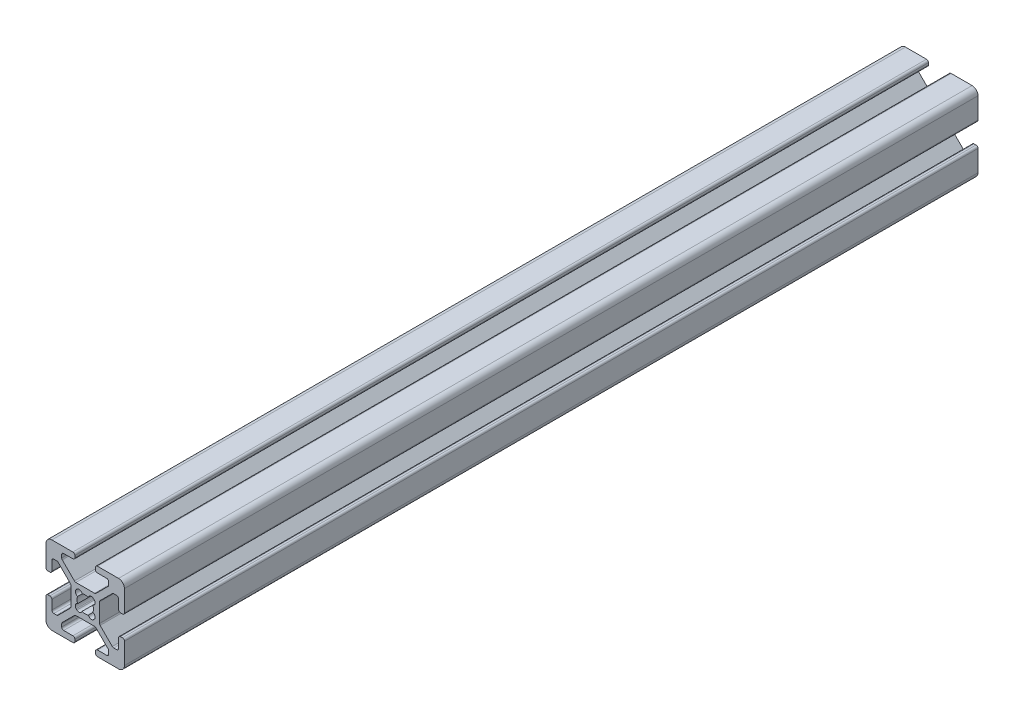
SolidWorks part; units mm, degrees
ref_plane "Front Plane" through (0, 0, 0) normal (0, 0, 1) x (1, 0, 0)
ref_plane "Top Plane" through (0, 0, 0) normal (0, 1, 0) x (1, 0, 0)
ref_plane "Right Plane" through (0, 0, 0) normal (1, 0, 0) x (0, 0, -1)
ref_plane "Plane1" through (0, 0, -4000) normal (0, 0, -1) x (-1, 0, 0)
sketch "Sketch1" plane through (0, 0, -4000) normal (0, 0, -1) x (-1, 0, 0)
  line L0 (2.3045, -2.1245) -> (2.1245, -2.3045)
  line L1 (-2.1245, -2.3045) -> (-2.3045, -2.1245)
  line L2 (-2.3045, 2.1245) -> (-2.1245, 2.3045)
  line L3 (2.1245, 2.3045) -> (2.3045, 2.1245)
  line L4 (10, -8.5) -> (10, -3.138)
  line L5 (9.492, -2.63) -> (9.008, -2.63)
  line L6 (8.5, -3.138) -> (8.5, -5.487)
  line L7 (7.992, -5.995) -> (7.2659, -5.995)
  line L8 (6.9067, -5.8462) -> (3.8038, -2.7433)
  line L9 (3.655, -2.3841) -> (3.655, 2.3838)
  line L10 (3.8038, 2.743) -> (6.907, 5.8462)
  line L11 (7.2662, 5.995) -> (7.992, 5.995)
  line L12 (8.5, 5.487) -> (8.5, 3.138)
  line L13 (9.008, 2.63) -> (9.492, 2.63)
  line L14 (10, 3.138) -> (10, 8.5)
  line L15 (8.5, 10) -> (3.138, 10)
  line L16 (2.63, 9.492) -> (2.63, 9.008)
  line L17 (3.138, 8.5) -> (5.487, 8.5)
  line L18 (5.995, 7.992) -> (5.995, 7.2659)
  line L19 (5.8462, 6.9067) -> (2.7433, 3.8038)
  line L20 (2.3841, 3.655) -> (-2.3838, 3.655)
  line L21 (-2.743, 3.8038) -> (-5.8462, 6.907)
  line L22 (-5.995, 7.2662) -> (-5.995, 7.992)
  line L23 (-5.487, 8.5) -> (-3.138, 8.5)
  line L24 (-2.63, 9.008) -> (-2.63, 9.492)
  line L25 (-3.138, 10) -> (-8.5, 10)
  line L26 (-10, 8.5) -> (-10, 3.138)
  line L27 (-9.492, 2.63) -> (-9.008, 2.63)
  line L28 (-8.5, 3.138) -> (-8.5, 5.487)
  line L29 (-7.992, 5.995) -> (-7.2659, 5.995)
  line L30 (-6.9067, 5.8462) -> (-3.8038, 2.7433)
  line L31 (-3.655, 2.3841) -> (-3.655, -2.3838)
  line L32 (-3.8038, -2.743) -> (-6.907, -5.8462)
  line L33 (-7.2662, -5.995) -> (-7.992, -5.995)
  line L34 (-8.5, -5.487) -> (-8.5, -3.138)
  line L35 (-9.008, -2.63) -> (-9.492, -2.63)
  line L36 (-10, -3.138) -> (-10, -8.5)
  line L37 (-8.5, -10) -> (-3.138, -10)
  line L38 (-2.63, -9.492) -> (-2.63, -9.008)
  line L39 (-3.138, -8.5) -> (-5.487, -8.5)
  line L40 (-5.995, -7.992) -> (-5.995, -7.2659)
  line L41 (-5.8462, -6.9067) -> (-2.7433, -3.8038)
  line L42 (-2.3841, -3.655) -> (2.3838, -3.655)
  line L43 (2.743, -3.8038) -> (5.8462, -6.907)
  line L44 (5.995, -7.2662) -> (5.995, -7.992)
  line L45 (5.487, -8.5) -> (3.138, -8.5)
  line L46 (2.63, -9.008) -> (2.63, -9.492)
  line L47 (3.138, -10) -> (8.5, -10)
  arc A0 (1.9358, 0.8037) -> (1.9358, -0.8037) centre (0, 0) cw
  arc A1 (1.9358, -0.8037) -> (2.3045, -2.1245) centre (1.748, -1.568) cw
  arc A2 (2.1245, -2.3045) -> (0.8037, -1.9358) centre (1.568, -1.748) cw
  arc A3 (0.8037, -1.9358) -> (-0.8037, -1.9358) centre (0, 0) cw
  arc A4 (-0.8037, -1.9358) -> (-2.1245, -2.3045) centre (-1.568, -1.748) cw
  arc A5 (-2.3045, -2.1245) -> (-1.9358, -0.8037) centre (-1.748, -1.568) cw
  arc A6 (-1.9358, -0.8037) -> (-1.9358, 0.8037) centre (0, 0) cw
  arc A7 (-1.9358, 0.8037) -> (-2.3045, 2.1245) centre (-1.748, 1.568) cw
  arc A8 (-2.1245, 2.3045) -> (-0.8037, 1.9358) centre (-1.568, 1.748) cw
  arc A9 (-0.8037, 1.9358) -> (0.8037, 1.9358) centre (0, 0) cw
  arc A10 (0.8037, 1.9358) -> (2.1245, 2.3045) centre (1.568, 1.748) cw
  arc A11 (2.3045, 2.1245) -> (1.9358, 0.8037) centre (1.748, 1.568) cw
  arc A12 (10, -3.138) -> (9.492, -2.63) centre (9.492, -3.138) ccw
  arc A13 (9.008, -2.63) -> (8.5, -3.138) centre (9.008, -3.138) ccw
  arc A14 (8.5, -5.487) -> (7.992, -5.995) centre (7.992, -5.487) cw
  arc A15 (7.2659, -5.995) -> (6.9067, -5.8462) centre (7.2659, -5.487) cw
  arc A16 (3.8038, -2.7433) -> (3.655, -2.3841) centre (4.163, -2.3841) cw
  arc A17 (3.655, 2.3838) -> (3.8038, 2.743) centre (4.163, 2.3838) cw
  arc A18 (6.907, 5.8462) -> (7.2662, 5.995) centre (7.2662, 5.487) cw
  arc A19 (7.992, 5.995) -> (8.5, 5.487) centre (7.992, 5.487) cw
  arc A20 (8.5, 3.138) -> (9.008, 2.63) centre (9.008, 3.138) ccw
  arc A21 (9.492, 2.63) -> (10, 3.138) centre (9.492, 3.138) ccw
  arc A22 (10, 8.5) -> (8.5, 10) centre (8.5, 8.5) ccw
  arc A23 (3.138, 10) -> (2.63, 9.492) centre (3.138, 9.492) ccw
  arc A24 (2.63, 9.008) -> (3.138, 8.5) centre (3.138, 9.008) ccw
  arc A25 (5.487, 8.5) -> (5.995, 7.992) centre (5.487, 7.992) cw
  arc A26 (5.995, 7.2659) -> (5.8462, 6.9067) centre (5.487, 7.2659) cw
  arc A27 (2.7433, 3.8038) -> (2.3841, 3.655) centre (2.3841, 4.163) cw
  arc A28 (-2.3838, 3.655) -> (-2.743, 3.8038) centre (-2.3838, 4.163) cw
  arc A29 (-5.8462, 6.907) -> (-5.995, 7.2662) centre (-5.487, 7.2662) cw
  arc A30 (-5.995, 7.992) -> (-5.487, 8.5) centre (-5.487, 7.992) cw
  arc A31 (-3.138, 8.5) -> (-2.63, 9.008) centre (-3.138, 9.008) ccw
  arc A32 (-2.63, 9.492) -> (-3.138, 10) centre (-3.138, 9.492) ccw
  arc A33 (-8.5, 10) -> (-10, 8.5) centre (-8.5, 8.5) ccw
  arc A34 (-10, 3.138) -> (-9.492, 2.63) centre (-9.492, 3.138) ccw
  arc A35 (-9.008, 2.63) -> (-8.5, 3.138) centre (-9.008, 3.138) ccw
  arc A36 (-8.5, 5.487) -> (-7.992, 5.995) centre (-7.992, 5.487) cw
  arc A37 (-7.2659, 5.995) -> (-6.9067, 5.8462) centre (-7.2659, 5.487) cw
  arc A38 (-3.8038, 2.7433) -> (-3.655, 2.3841) centre (-4.163, 2.3841) cw
  arc A39 (-3.655, -2.3838) -> (-3.8038, -2.743) centre (-4.163, -2.3838) cw
  arc A40 (-6.907, -5.8462) -> (-7.2662, -5.995) centre (-7.2662, -5.487) cw
  arc A41 (-7.992, -5.995) -> (-8.5, -5.487) centre (-7.992, -5.487) cw
  arc A42 (-8.5, -3.138) -> (-9.008, -2.63) centre (-9.008, -3.138) ccw
  arc A43 (-9.492, -2.63) -> (-10, -3.138) centre (-9.492, -3.138) ccw
  arc A44 (-10, -8.5) -> (-8.5, -10) centre (-8.5, -8.5) ccw
  arc A45 (-3.138, -10) -> (-2.63, -9.492) centre (-3.138, -9.492) ccw
  arc A46 (-2.63, -9.008) -> (-3.138, -8.5) centre (-3.138, -9.008) ccw
  arc A47 (-5.487, -8.5) -> (-5.995, -7.992) centre (-5.487, -7.992) cw
  arc A48 (-5.995, -7.2659) -> (-5.8462, -6.9067) centre (-5.487, -7.2659) cw
  arc A49 (-2.7433, -3.8038) -> (-2.3841, -3.655) centre (-2.3841, -4.163) cw
  arc A50 (2.3838, -3.655) -> (2.743, -3.8038) centre (2.3838, -4.163) cw
  arc A51 (5.8462, -6.907) -> (5.995, -7.2662) centre (5.487, -7.2662) cw
  arc A52 (5.995, -7.992) -> (5.487, -8.5) centre (5.487, -7.992) cw
  arc A53 (3.138, -8.5) -> (2.63, -9.008) centre (3.138, -9.008) ccw
  arc A54 (2.63, -9.492) -> (3.138, -10) centre (3.138, -9.492) ccw
  arc A55 (8.5, -10) -> (10, -8.5) centre (8.5, -8.5) ccw
extrude "Boss-Extrude1" add sketch "Sketch1" against normal blind 217.678
